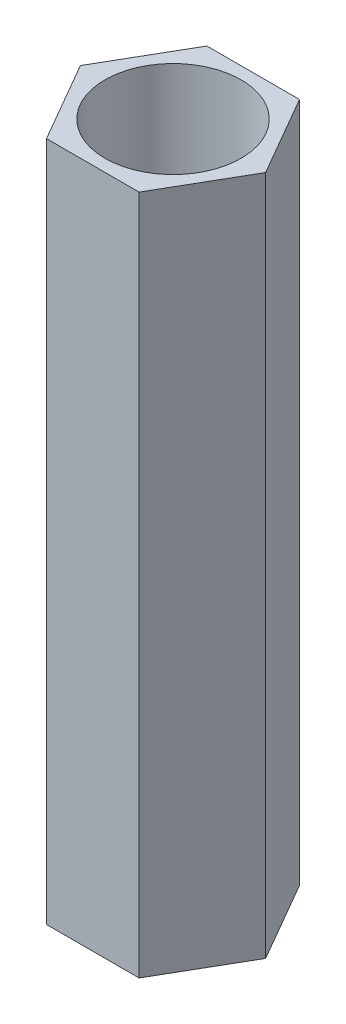
SolidWorks part; units mm, degrees
ref_plane "Front Plane" through (0, 0, 0) normal (0, 0, 1) x (1, 0, 0)
ref_plane "Top Plane" through (0, 0, 0) normal (0, 1, 0) x (1, 0, 0)
ref_plane "Right Plane" through (0, 0, 0) normal (1, 0, 0) x (0, 0, -1)
sketch "Sketch1" plane through (0, 0, 0) normal (0, 1, 0) x (1, 0, 0)
  line L1 (1.9053, 0) -> (0.9526, 1.65)
  line L2 (0.9526, 1.65) -> (-0.9526, 1.65)
  line L3 (-0.9526, 1.65) -> (-1.9053, 0)
  line L4 (-1.9053, 0) -> (-0.9526, -1.65)
  line L5 (-0.9526, -1.65) -> (0.9526, -1.65)
  line L6 (0.9526, -1.65) -> (1.9053, 0)
  circle A0 centre (0, 0) radius 1.65 construction
  circle A1 centre (0, 0) radius 1.4
  dimension "D1" = 2.8
  dimension "D2" = 3.3
extrude "Boss-Extrude1" add sketch "Sketch1" along normal blind 14
